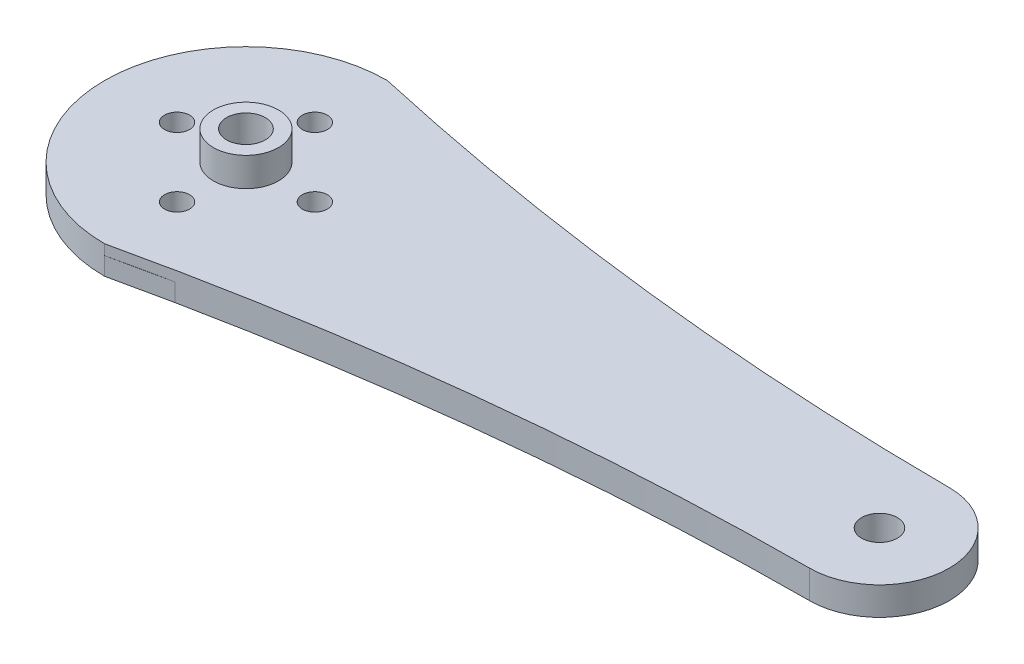
SolidWorks part; units mm, degrees
ref_plane "Front Plane" through (0, 0, 0) normal (0, 0, 1) x (1, 0, 0)
ref_plane "Top Plane" through (0, 0, 0) normal (0, 1, 0) x (1, 0, 0)
ref_plane "Right Plane" through (0, 0, 0) normal (1, 0, 0) x (0, 0, -1)
sketch "Sketch1" plane through (0, 0, 0) normal (0, 1, 0) x (1, 0, 0)
  line L0 (0, 15.5) -> (0, -15.5) construction
  line L1 (-15.5, 0) -> (15.5, 0) construction
  line L2 (-2.4674, 13.4022) -> (-4, 4) construction
  line L3 (4, -4) -> (-4, -4) construction
  line L4 (4, -4) -> (4, 4) construction
  line L5 (4, 4) -> (-4, 4) construction
  line L6 (-4, -4) -> (-4, 4) construction
  line L7 (4, -4) -> (-4, 4) construction
  line L8 (4, 4) -> (-4, -4) construction
  line L9 (-4, 4) -> (-2.4674, 13.4022)
  line L10 (4, 4) -> (2.4674, 13.4022)
  line L11 (4, -4) -> (2.4674, -13.4022)
  line L12 (-4, -4) -> (-2.4674, -13.4022)
  line L13 (-4, 4) -> (-12.5927, 2.4331) construction
  line L14 (-4, 4) -> (-12.4485, 2.4594)
  line L15 (-4, -4) -> (-12.4485, -2.4594)
  line L16 (4, -4) -> (12.4485, -2.4594)
  line L17 (4, 4) -> (12.4485, 2.4594)
  circle A0 centre (0, 0) radius 15.5 construction
  circle A1 centre (0, 0) radius 14.5 construction
  arc A2 (2.4674, 13.4022) -> (-2.4674, 13.4022) centre (0, 13) ccw
  arc A3 (2.4674, -13.4022) -> (-2.4674, -13.4022) centre (0, -13) cw
  arc A4 (-12.4485, 2.4594) -> (-12.4485, -2.4594) centre (-12, 0) ccw
  arc A5 (12.4485, 2.4594) -> (12.4485, -2.4594) centre (12, 0) cw
  circle A6 centre (0, 0) radius 12 construction
  circle A7 centre (0, 0) radius 9.5 construction
  circle A8 centre (0, 0) radius 7.5 construction
  circle A9 centre (0, 12) radius 0.5
  circle A10 centre (0, 9.5) radius 0.5
  circle A11 centre (0, 7.5) radius 0.5
  circle A12 centre (12, 0) radius 0.5
  circle A13 centre (9.5, 0) radius 0.5
  circle A14 centre (7.5, 0) radius 0.5
  circle A15 centre (0, -12) radius 0.5
  circle A16 centre (0, -9.5) radius 0.5
  circle A17 centre (0, -7.5) radius 0.5
  circle A18 centre (-12, 0) radius 0.5
  circle A19 centre (-9.5, 0) radius 0.5
  circle A20 centre (-7.5, 0) radius 0.5
  circle A21 centre (0, 0) radius 1.375
  point P59 (0, 0)
  dimension "D1" = 31
  dimension "D2" = 1
  dimension "D3" = 5
  dimension "D4" = 5
  dimension "D5" = 8
  dimension "D6" = 8
  dimension "D7" = 15
  dimension "D9" = 24
  dimension "D11" = 1
  dimension "D12" = 1
  dimension "D13" = 4
  dimension "D8" = 19
  dimension "D10" = 1
  dimension "D14" = 2.75
extrude "Boss-Extrude1" add sketch "Sketch1" along normal blind 2
sketch "Sketch4" plane through (0, 0, 0) normal (0, -1, 0) x (1, 0, 0)
  circle A0 centre (0, 0) radius 4.627
  circle A1 centre (0, 0) radius 2.627
  dimension "D1" = 9.254
  dimension "D2" = 2
extrude "Boss-Extrude3" add sketch "Sketch4" along normal blind 2.5
sketch "Sketch6" plane through (0, 2, 0) normal (0, 1, 0) x (1, 0, 0)
  circle A0 centre (0, 0) radius 20.066
  circle A2 centre (0, 0) radius 3.75
  dimension "D1" = 40.132
extrude "Boss-Extrude6" add sketch "Sketch6" against normal blind 2.54
sketch "Sketch7" plane through (0, 2, 0) normal (0, 1, 0) x (1, 0, 0)
  circle A0 centre (0, 9.779) radius 1.778
extrude "Cut-Extrude4" cut sketch "Sketch7" against normal blind 2.54
pattern_circular "CirPattern1" count 4 over 360 about axis through (0, 0, 0) along (0, 1, 0) of "Cut-Extrude4"
sketch "Esquisse1" plane through (0, 2, 0) normal (0, 1, 0) x (1, 0, 0)
  arc A0 (89.916, 9.906) -> (89.916, -9.906) centre (89.916, 0) cw
  arc A1 (0, 20.066) -> (89.916, 9.906) centre (91.4526, 426.4632) ccw
  circle A2 centre (0, 0) radius 20.066 construction
  arc A3 (89.916, -9.906) -> (0, -20.066) centre (91.4526, -426.4632) ccw
  arc A5 (0, 20.066) -> (0, -20.066) centre (-8.4657, 0) cw
  dimension "D6" = 416.56
  dimension "D7" = 416.56
  dimension "D2" = 9.906
  dimension "D1" = 89.916
extrude "Boss.-Extru.1" add sketch "Esquisse1" along normal blind 2.2225 and the other way blind 2.54 contours A1 A0 A3 A5
sketch "Esquisse2" plane through (0, 2, 0) normal (0, 1, 0) x (1, 0, 0)
  line L0 (8.2277, -18.3016) -> (0, -20.066)
  line L1 (8.2277, 18.3016) -> (0, 20.066)
  arc A0 (8.2277, -18.3016) -> (0, -20.066) centre (0, 0) cw
  arc A1 (0, 20.066) -> (8.2277, 18.3016) centre (0, 0) cw
extrude "Enlèv. mat.-Extru.1" cut sketch "Esquisse2" against normal up to next
sketch "Esquisse3" plane through (0, 2, 0) normal (0, 1, 0) x (1, 0, 0)
  arc A0 (0, -20.066) -> (0, 20.066) centre (-8.4657, 0) ccw
  arc A1 (0, -20.066) -> (0, 20.066) centre (0, 0) cw
  circle A2 centre (0, 0) radius 1.375
  circle A3 centre (0, 9.779) radius 1.778
  circle A4 centre (9.779, 0) radius 1.778
  circle A5 centre (0, -9.779) radius 1.778
  circle A6 centre (-9.779, 0) radius 1.778
extrude "Boss.-Extru.2" add sketch "Esquisse3" along normal blind 2.2225
sketch "Esquisse4" plane through (0, -0.54, 0) normal (0, -1, 0) x (-1, 0, 0)
  circle A0 centre (-89.916, 0) radius 2.54
  dimension "D1" = 5.08
extrude "Enlèv. mat.-Extru.2" cut sketch "Esquisse4" against normal up to next
sketch "Esquisse8" plane through (0, 4.2225, 0) normal (0, 1, 0) x (1, 0, 0)
  line L1 (-30.1323, -30.8902) -> (110.7262, -30.8902)
  line L2 (-30.1323, -30.8902) -> (-30.1323, 29.7858)
  line L3 (-30.1323, 29.7858) -> (110.7262, 29.7858)
  line L4 (110.7262, -30.8902) -> (110.7262, 29.7858)
extrude "Enlèv. mat.-Extru.6" cut sketch "Esquisse8" against normal blind 0.76
sketch "Esquisse9" plane through (0, 3.4625, 0) normal (0, 1, 0) x (1, 0, 0)
  circle A0 centre (0, 0) radius 4.625
  dimension "D1" = 9.25
extrude "Boss.-Extru.3" add sketch "Esquisse9" along normal blind 4.1
sketch "Sketch5" plane through (0, -2.5, 0) normal (0, -1, 0) x (1, 0, 0)
  line L0 (0, 0) -> (0, 0.6245) construction
  line L1 (0, 3.1016) -> (-0.2828, 2.6117)
  line L2 (0, 3.1016) -> (0.2828, 2.6117)
  line L3 (0.9584, 2.9498) -> (0.5381, 2.5713)
  line L4 (0.9584, 2.9498) -> (1.076, 2.3965)
  line L5 (1.8231, 2.5092) -> (1.3063, 2.2792)
  line L6 (1.8231, 2.5092) -> (1.7639, 1.9467)
  line L7 (2.5092, 1.8231) -> (1.9467, 1.7639)
  line L8 (2.5092, 1.8231) -> (2.2792, 1.3063)
  line L9 (2.9498, 0.9584) -> (2.3965, 1.076)
  line L10 (2.9498, 0.9584) -> (2.5713, 0.5381)
  line L11 (3.1016, 0) -> (2.6117, 0.2828)
  line L12 (3.1016, 0) -> (2.6117, -0.2828)
  line L13 (2.9498, -0.9584) -> (2.5713, -0.5381)
  line L14 (2.9498, -0.9584) -> (2.3965, -1.076)
  line L15 (2.5092, -1.8231) -> (2.2792, -1.3063)
  line L16 (2.5092, -1.8231) -> (1.9467, -1.7639)
  line L17 (1.8231, -2.5092) -> (1.7639, -1.9467)
  line L18 (1.8231, -2.5092) -> (1.3063, -2.2792)
  line L19 (0.9584, -2.9498) -> (1.076, -2.3965)
  line L20 (0.9584, -2.9498) -> (0.5381, -2.5713)
  line L21 (0, -3.1016) -> (0.2828, -2.6117)
  line L22 (0, -3.1016) -> (-0.2828, -2.6117)
  line L23 (-0.9584, -2.9498) -> (-0.5381, -2.5713)
  line L24 (-0.9584, -2.9498) -> (-1.076, -2.3965)
  line L25 (-1.8231, -2.5092) -> (-1.3063, -2.2792)
  line L26 (-1.8231, -2.5092) -> (-1.7639, -1.9467)
  line L27 (-2.5092, -1.8231) -> (-1.9467, -1.7639)
  line L28 (-2.5092, -1.8231) -> (-2.2792, -1.3063)
  line L29 (-2.9498, -0.9584) -> (-2.3965, -1.076)
  line L30 (-2.9498, -0.9584) -> (-2.5713, -0.5381)
  line L31 (-3.1016, 0) -> (-2.6117, -0.2828)
  line L32 (-3.1016, 0) -> (-2.6117, 0.2828)
  line L33 (-2.9498, 0.9584) -> (-2.5713, 0.5381)
  line L34 (-2.9498, 0.9584) -> (-2.3965, 1.076)
  line L35 (-2.5092, 1.8231) -> (-2.2792, 1.3063)
  line L36 (-2.5092, 1.8231) -> (-1.9467, 1.7639)
  line L37 (-1.8231, 2.5092) -> (-1.7639, 1.9467)
  line L38 (-1.8231, 2.5092) -> (-1.3063, 2.2792)
  line L39 (-0.9584, 2.9498) -> (-1.076, 2.3965)
  line L40 (-0.9584, 2.9498) -> (-0.5381, 2.5713)
  circle A0 centre (0, 0) radius 2.627 construction
  arc A1 (-2.2792, 1.3063) -> (-2.3965, 1.076) centre (0, 0) ccw
  arc A2 (-1.7639, 1.9467) -> (-1.9467, 1.7639) centre (0, 0) ccw
  arc A3 (-1.076, 2.3965) -> (-1.3063, 2.2792) centre (0, 0) ccw
  arc A4 (-0.2828, 2.6117) -> (-0.5381, 2.5713) centre (0, 0) ccw
  arc A5 (0.5381, 2.5713) -> (0.2828, 2.6117) centre (0, 0) ccw
  arc A6 (1.3063, 2.2792) -> (1.076, 2.3965) centre (0, 0) ccw
  arc A7 (1.9467, 1.7639) -> (1.7639, 1.9467) centre (0, 0) ccw
  arc A8 (2.3965, 1.076) -> (2.2792, 1.3063) centre (0, 0) ccw
  arc A9 (2.6117, 0.2828) -> (2.5713, 0.5381) centre (0, 0) ccw
  arc A10 (2.5713, -0.5381) -> (2.6117, -0.2828) centre (0, 0) ccw
  arc A11 (2.2792, -1.3063) -> (2.3965, -1.076) centre (0, 0) ccw
  arc A12 (1.7639, -1.9467) -> (1.9467, -1.7639) centre (0, 0) ccw
  arc A13 (1.076, -2.3965) -> (1.3063, -2.2792) centre (0, 0) ccw
  arc A14 (0.2828, -2.6117) -> (0.5381, -2.5713) centre (0, 0) ccw
  arc A15 (-0.5381, -2.5713) -> (0, -2.627) centre (0, 0) ccw
  arc A16 (-1.3063, -2.2792) -> (-1.076, -2.3965) centre (0, 0) ccw
  arc A17 (-1.9467, -1.7639) -> (-1.7639, -1.9467) centre (0, 0) ccw
  arc A18 (-2.3965, -1.076) -> (-2.2792, -1.3063) centre (0, 0) ccw
  arc A19 (-2.6117, -0.2828) -> (-2.5713, -0.5381) centre (0, 0) ccw
  arc A20 (-2.5713, 0.5381) -> (-2.6117, 0.2828) centre (0, 0) ccw
  point P68 (0, 0)
  circle M5 centre (0, 0) radius 2.627
  dimension "D1" = 30
  dimension "D2" = 3.1016
  dimension "D3" = 20
extrude "Cut-Extrude3" cut sketch "Sketch5" against normal blind 3.3 contours L36 L35 M5 | L34 L33 M5 | L32 L31 M5 | L30 L29 M5 | L28 L27 M5 | L26 L25 M5 | L24 L23 M5 | L0 L21 M5 | L22 L0 M5 | L20 L19 M5 | L18 L17 M5 | L16 L15 M5 | L14 L13 M5 | L12 L11 M5 | L10 L9 M5 | L8 L7 M5 | L6 L5 M5 | L4 L3 M5 | L0 L2 M5 | L0 L1 M5 | L40 L39 M5 | L38 L37 M5
sketch "Esquisse10" plane through (0, 0, 0) normal (0, -1, 0) x (-1, 0, 0)
  circle A0 centre (0, 0) radius 2.627
  circle A1 centre (0, 0) radius 1.375
extrude "Enlèv. mat.-Extru.8" cut sketch "Esquisse10" against normal blind 0.8
sketch "Esquisse11" plane through (0, 3.4625, 0) normal (0, -1, 0) x (-1, 0, 0)
  circle A0 centre (0, 0) radius 1.375
extrude "Enlèv. mat.-Extru.9" cut sketch "Esquisse11" against normal blind 10
sketch "Esquisse12" plane through (0, 7.5625, 0) normal (0, 1, 0) x (1, 0, 0)
  circle A0 centre (0, 0) radius 2.75
extrude "Enlèv. mat.-Extru.10" cut sketch "Esquisse12" against normal blind 5.86
